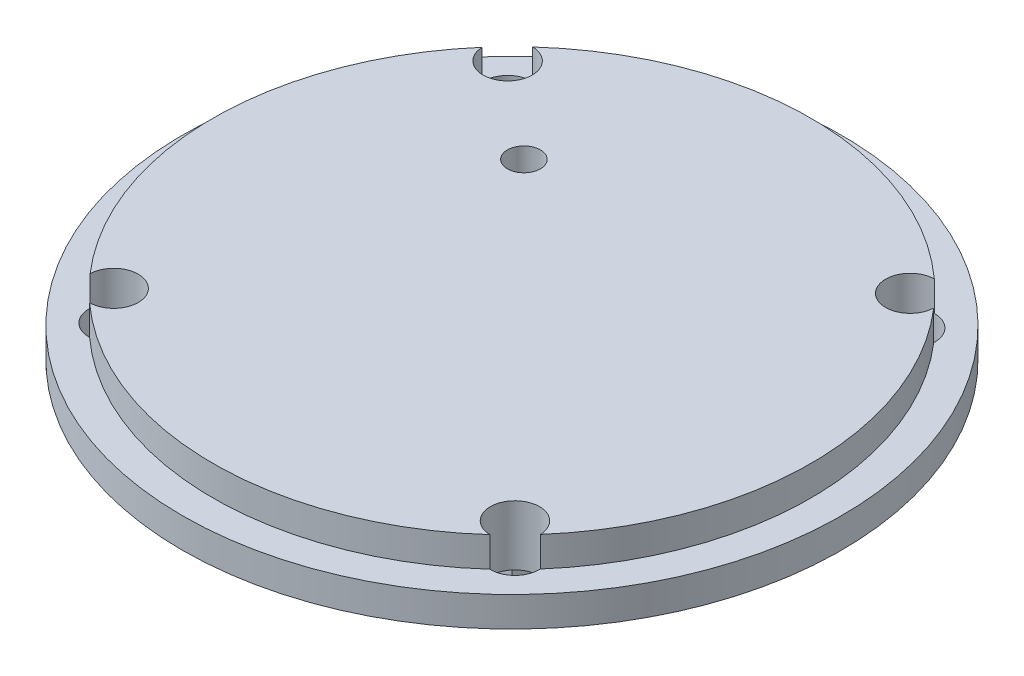
SolidWorks part; units mm, degrees
ref_plane "Спереди" through (0, 0, 0) normal (0, 0, 1) x (1, 0, 0)
ref_plane "Сверху" through (0, 0, 0) normal (0, 1, 0) x (1, 0, 0)
ref_plane "Справа" through (0, 0, 0) normal (1, 0, 0) x (0, 0, -1)
sketch "Эскиз1" plane through (0, 0, 0) normal (0, 1, 0) x (1, 0, 0)
  circle A0 centre (0, 0) radius 55
  dimension "D1" = 110
extrude "Бобышка-Вытянуть1" add sketch "Эскиз1" along normal blind 5
sketch "Эскиз2" plane through (0, 5, 0) normal (0, 1, 0) x (1, 0, 0)
  circle A0 centre (0, 0) radius 49.9
  dimension "D1" = 99.8
extrude "Бобышка-Вытянуть2" add sketch "Эскиз2" along normal blind 5
sketch "Эскиз3" plane through (0, 0, 0) normal (0, -1, 0) x (1, 0, 0)
  line L1 (15, -15) -> (-15, -15)
  line L2 (15, -15) -> (15, 15)
  line L3 (15, 15) -> (-15, 15)
  line L4 (-15, -15) -> (-15, 15)
  line L5 (15, -15) -> (-15, 15) construction
  line L6 (15, 15) -> (-15, -15) construction
  point P0 (0, 0)
  dimension "D1" = 30
  dimension "D2" = 30
extrude "Бобышка-Вытянуть3" add sketch "Эскиз3" along normal blind 20
sketch "Эскиз4" plane through (0, 0, 15) normal (0, 0, 1) x (1, 0, 0)
  line L0 (-15, 0) -> (15, -20) construction
  line L2 (10.1, -15.1) -> (-10.1, -15.1)
  line L3 (10.1, -15.1) -> (10.1, -4.9)
  line L4 (10.1, -4.9) -> (-10.1, -4.9)
  line L5 (-10.1, -15.1) -> (-10.1, -4.9)
  line L6 (10.1, -15.1) -> (-10.1, -4.9) construction
  line L7 (10.1, -4.9) -> (-10.1, -15.1) construction
  point P4 (0, -10)
  dimension "D1" = 20.2
  dimension "D2" = 10.2
extrude "Вырез-Вытянуть1" cut sketch "Эскиз4" against normal through all
sketch "Эскиз5" plane through (0, 0, 0) normal (0, -1, 0) x (1, 0, 0)
  line L0 (23.35, -22.85) -> (39.3102, -38.467) construction
  line L5 (-23.35, 22.85) -> (23.35, -22.85) construction
  line L6 (-23.35, -22.85) -> (23.35, 22.85) construction
  line L7 (-23.35, 22.85) -> (-39.3095, 38.4677) construction
  line L8 (23.35, 22.85) -> (39.1401, 38.6401) construction
  line L9 (-23.35, -22.85) -> (-39.3095, -38.4677) construction
  circle A0 centre (0, 0) radius 55 construction
  circle A1 centre (33.5922, -32.8719) radius 4.1
  circle A2 centre (-33.5917, -32.8724) radius 4.1
  circle A3 centre (-33.5917, 32.8724) radius 4.1
  circle A4 centre (33.4832, 32.9832) radius 4.1
  point P0 (0, 0)
  dimension "D3" = 8.2
  dimension "D1" = 46.7
  dimension "D2" = 45.7
  dimension "D4" = 8
  dimension "D5" = 8
  dimension "D6" = 8
  dimension "D7" = 8
extrude "Вырез-Вытянуть2" cut sketch "Эскиз5" against normal through all
sketch "Эскиз6" plane through (0, 10, 0) normal (0, 1, 0) x (1, 0, 0)
  line L0 (0, 0) -> (0.0004, 49.9) construction
  line L1 (0.0001, 20) -> (-17.9999, 20) construction
  arc A0 (33.5133, 36.9712) -> (-33.5128, 36.9717) centre (0, 0) ccw construction
  circle A1 centre (-17.9999, 20) radius 2.75
  dimension "D3" = 5.5
  dimension "D1" = 20
  dimension "D2" = 18
extrude "Вырез-Вытянуть3" cut sketch "Эскиз6" against normal through all
